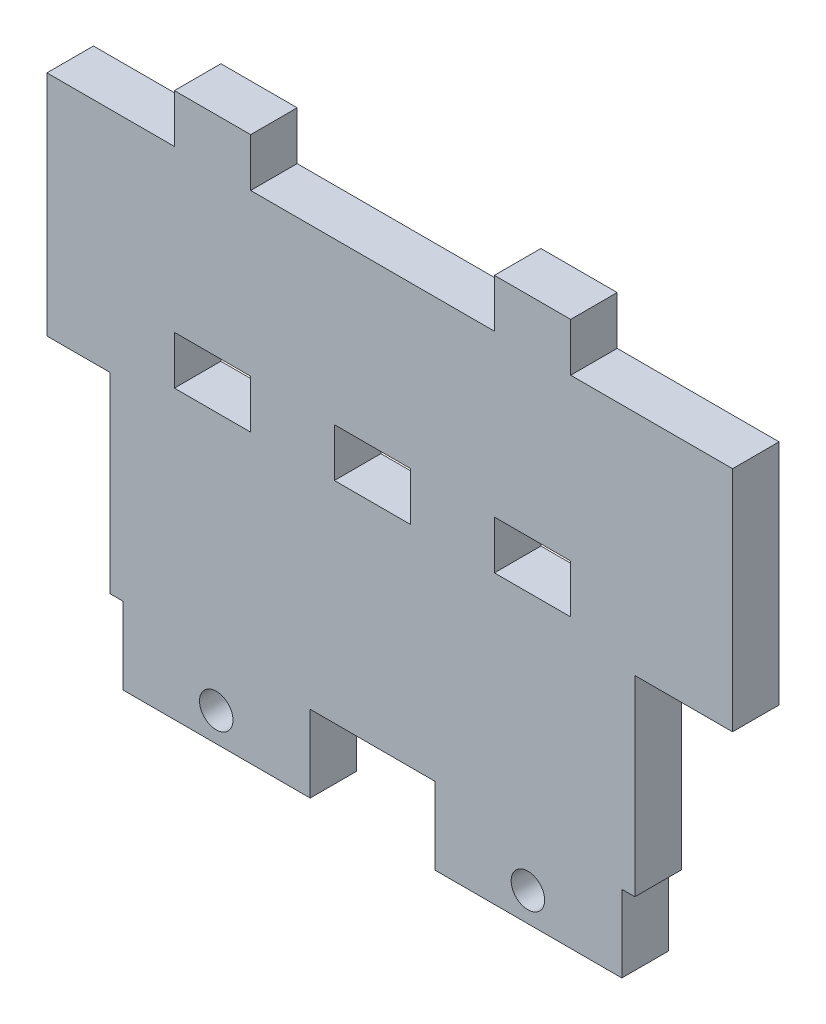
SolidWorks part; units mm, degrees
ref_plane "Front Plane" through (0, 0, 0) normal (0, 0, 1) x (1, 0, 0)
ref_plane "Top Plane" through (0, 0, 0) normal (0, 1, 0) x (1, 0, 0)
ref_plane "Right Plane" through (0, 0, 0) normal (1, 0, 0) x (0, 0, -1)
sketch "Sketch1" plane through (0, 0, 0) normal (0, 0, 1) x (1, 0, 0)
  line L0 (26.9176, -2.0915) -> (33.7176, -2.0915)
  line L1 (-36.2824, 22.4085) -> (33.7176, 22.4085)
  line L2 (-36.2824, 22.4085) -> (-36.2824, -2.0915)
  line L3 (-36.2824, -2.0915) -> (-29.4824, -2.0915)
  line L4 (33.7176, 22.4085) -> (33.7176, -2.0915)
  line L5 (-7.9824, -22.6915) -> (5.4176, -22.6915)
  line L6 (-29.4824, -2.0915) -> (-29.4824, -22.6915)
  line L7 (-29.4824, -22.6915) -> (-28.0824, -22.6915)
  line L8 (26.9176, -2.0915) -> (26.9176, -22.6915)
  line L9 (25.5176, -22.6915) -> (26.9176, -22.6915)
  line L10 (-28.0824, -22.6915) -> (-28.0824, -30.9557)
  line L11 (-28.0824, -30.9557) -> (-7.9824, -30.9557)
  line L12 (-7.9824, -22.6915) -> (-7.9824, -30.9557)
  line L14 (5.4176, -22.6915) -> (5.4176, -30.9557)
  line L15 (5.4176, -30.9557) -> (25.5176, -30.9557)
  line L16 (25.5176, -22.6915) -> (25.5176, -30.9557)
  point P21 (-18.0324, -30.9557)
  dimension "D1" = 70
  dimension "D2" = 24.5
  dimension "D3" = 6.8
  dimension "D4" = 1.4
  dimension "D5" = 20.1
  dimension "D6" = 20.6
  dimension "D7" = 28.8642
extrude "Boss-Extrude1" add sketch "Sketch1" along normal blind 5 contours L1 L4 L0 L8 L9 L16 L15 L14 L5 L12 L11 L10 L7 L6 L3 L2
sketch "Sketch2" plane through (0, 0, 5) normal (0, 0, 1) x (1, 0, 0)
  line L0 (-8.8824, 2.5085) -> (-36.2824, 2.5085) construction
  line L1 (-22.5824, 5.1085) -> (-14.3824, 5.1085)
  line L2 (-22.5824, 5.1085) -> (-22.5824, -0.0915)
  line L3 (-22.5824, -0.0915) -> (-14.3824, -0.0915)
  line L4 (-14.3824, 5.1085) -> (-14.3824, -0.0915)
  line L5 (-36.2824, 22.4085) -> (-36.2824, -2.0915) construction
  line L6 (33.7176, 22.4085) -> (33.7176, -2.0915) construction
  line L7 (-36.2824, -2.0915) -> (-29.4824, -2.0915) construction
  line L8 (-5.3824, 5.1085) -> (2.8176, 5.1085)
  line L9 (-5.3824, 5.1085) -> (-5.3824, -0.0915)
  line L10 (-5.3824, -0.0915) -> (2.8176, -0.0915)
  line L11 (2.8176, 5.1085) -> (2.8176, -0.0915)
  line L12 (-1.2824, 5.1085) -> (-1.2824, -0.0915) construction
  line L13 (11.8176, 5.1085) -> (20.0176, 5.1085)
  line L14 (11.8176, 5.1085) -> (11.8176, -0.0915)
  line L15 (11.8176, -0.0915) -> (20.0176, -0.0915)
  line L16 (20.0176, 5.1085) -> (20.0176, -0.0915)
  line L17 (-28.0824, -30.9557) -> (-7.9824, -30.9557) construction
  line L25 (8.3176, 2.5085) -> (-19.0824, 2.5085) construction
  line L26 (25.5176, 2.5085) -> (-1.8824, 2.5085) construction
  line L27 (42.7176, 2.5085) -> (15.3176, 2.5085) construction
  line L28 (29.0176, 5.1085) -> (37.2176, 5.1085) [skipped]
  line L29 (29.0176, 5.1085) -> (29.0176, -0.0915) [skipped]
  line L30 (29.0176, -0.0915) -> (37.2176, -0.0915) [skipped]
  line L31 (37.2176, 5.1085) -> (37.2176, -0.0915) [skipped]
  circle A0 centre (15.4176, -27.8557) radius 1.8
  circle A1 centre (-18.0824, -27.8557) radius 1.8
  point P9 (-22.5824, 2.5085)
  point P11 (29.0176, 2.5085)
  point P18 (-5.3824, 2.5085)
  point P25 (11.8176, 2.5085)
  dimension "D7" = 3.6
  dimension "D10" = 33.5
  dimension "D3" = 5.2
  dimension "D4" = 4
  dimension "D5" = 9
  dimension "D6" = 35
  dimension "D1" = 4.6
  dimension "D2" = 8.2
  dimension "D8" = 3.1
  dimension "D9" = 18.3
extrude "Cut-Extrude1" cut sketch "Sketch2" against normal up to next
sketch "Sketch3" plane through (0, 0, 5) normal (0, 0, 1) x (1, 0, 0)
  line L0 (-36.2824, 22.4085) -> (33.7176, 22.4085) construction
  line L1 (33.7176, 22.4085) -> (37.4176, 22.4085)
  line L2 (33.7176, 22.4085) -> (33.7176, -2.0915)
  line L3 (33.7176, -2.0915) -> (37.4176, -2.0915)
  line L4 (37.4176, 22.4085) -> (37.4176, -2.0915)
  line L5 (26.9176, -2.0915) -> (33.7176, -2.0915) construction
  dimension "D1" = 3.7
extrude "Boss-Extrude4" add sketch "Sketch3" against normal blind 5
sketch "Sketch4" plane through (0, 0, 5) normal (0, 0, 1) x (1, 0, 0)
  line L0 (-36.2824, 22.4085) -> (37.4176, 22.4085) construction
  line L1 (-22.5824, 22.4085) -> (-14.3824, 22.4085)
  line L2 (-22.5824, 22.4085) -> (-22.5824, 27.6085)
  line L3 (-22.5824, 27.6085) -> (-14.3824, 27.6085)
  line L4 (-14.3824, 22.4085) -> (-14.3824, 27.6085)
  line L5 (-22.5824, 5.1085) -> (-22.5824, -0.0915) construction
  line L6 (11.8176, 22.4085) -> (20.0176, 22.4085)
  line L7 (11.8176, 22.4085) -> (11.8176, 27.6085)
  line L8 (11.8176, 27.6085) -> (20.0176, 27.6085)
  line L9 (20.0176, 22.4085) -> (20.0176, 27.6085)
  line L10 (-14.3824, -0.0915) -> (-14.3824, 5.1085) construction
  line L11 (11.8176, 5.1085) -> (11.8176, -0.0915) construction
  line L12 (20.0176, -0.0915) -> (20.0176, 5.1085) construction
extrude "Boss-Extrude7" add sketch "Sketch4" against normal up to surface (5 mm away) up to face at (-16.2824, -27.8557, 0)
